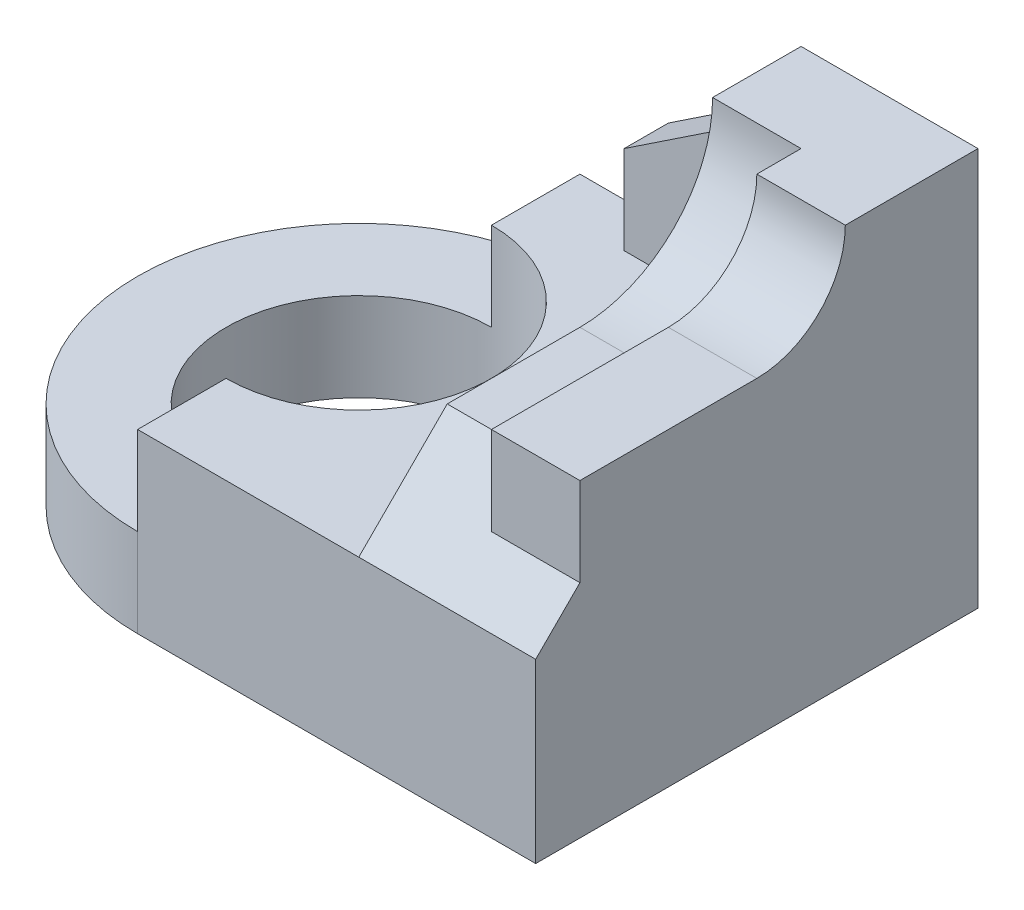
SolidWorks part; units mm, degrees
ref_plane "Front Plane" through (0, 0, 0) normal (0, 0, 1) x (1, 0, 0)
ref_plane "Top Plane" through (0, 0, 0) normal (0, 1, 0) x (1, 0, 0)
ref_plane "Right Plane" through (0, 0, 0) normal (1, 0, 0) x (0, 0, -1)
sketch "Sketch2" plane through (0, 0, 0) normal (0, 1, 0) x (1, 0, 0)
  line L1 (0, 0) -> (-140, 0)
  line L2 (0, 0) -> (0, 100)
  line L3 (0, 100) -> (-140, 100)
  line L4 (-140, 0) -> (-140, 100)
  dimension "D1" = 140
  dimension "D2" = 100
extrude "Boss-Extrude2" add sketch "Sketch2" along normal blind 90
sketch "Sketch3" plane through (0, 90, 0) normal (0, 1, 0) x (1, 0, 0)
  line L0 (0, 100) -> (-140, 100) construction
  line L1 (-140, 100) -> (-140, 0) construction
  line L4 (-90, 100) -> (-140, 100)
  line L5 (-140, 100) -> (-140, 0)
  line L6 (-140, 0) -> (-90, 0)
  arc A0 (-90, 100) -> (-90, 0) centre (-90, 50) ccw
  line M2 (0, 100) -> (-140, 100)
  line M3 (-140, 100) -> (-140, 0)
  line M4 (-140, 0) -> (0, 0)
  dimension "D1" = 50
extrude "Cut-Extrude1" cut sketch "Sketch3" against normal blind 90 contours A0 M2 M3 | A0 L5 M4
sketch "Sketch4" plane through (0, 90, 0) normal (0, 1, 0) x (1, 0, 0)
  circle A0 centre (-90, 50) radius 30
  arc A1 (-90, 100) -> (-90, 0) centre (-90, 50) ccw construction
  point P2 (-140, 50)
  dimension "D1" = 60
  dimension "D2" = 50
  dimension "D3" = 50
extrude "Cut-Extrude2" cut sketch "Sketch4" against normal blind 90
ref_plane "Plane1" through (0, 20, 0) normal (0, 1, 0) x (1, 0, 0)
sketch "Sketch5" plane through (0, 20, 0) normal (0, 1, 0) x (1, 0, 0)
  line L1 (-90, 0) -> (-140, 0)
  line L2 (-90, 0) -> (-90, 100)
  line L3 (-90, 100) -> (-140, 100)
  line L4 (-140, 0) -> (-140, 100)
  dimension "D1" = 90
  dimension "D2" = 0
  dimension "D3" = 0
  dimension "D4" = 50
extrude "Cut-Extrude3" cut sketch "Sketch5" along normal blind 90
ref_plane "Plane2" through (0, 40, 0) normal (0, 1, 0) x (1, 0, 0)
sketch "Sketch6" plane through (0, 40, 0) normal (0, 1, 0) x (1, 0, 0)
  line L0 (0, 100) -> (-90, 100) construction
  line L1 (-40, 0) -> (-90, 0)
  line L2 (-40, 0) -> (-40, 100)
  line L3 (-40, 100) -> (-90, 100)
  line L4 (-90, 0) -> (-90, 100)
  line L5 (-90, 0) -> (0, 0) construction
  dimension "D1" = 40
  dimension "D2" = 0
  dimension "D3" = 0
  dimension "D4" = 50
extrude "Cut-Extrude4" cut sketch "Sketch6" along normal blind 90
sketch "Sketch7" plane through (-40, 0, 0) normal (-1, 0, 0) x (0, 0, 1)
  line L0 (-100, 90) -> (0, 90) construction
  line L1 (-50, 60) -> (0, 60)
  line L2 (0, 90) -> (0, 40) construction
  line L3 (-80, 90) -> (0, 90)
  line L4 (0, 90) -> (0, 60)
  arc A0 (-80, 90) -> (-50, 60) centre (-50, 90) ccw
  dimension "D1" = 30
  dimension "D2" = 20
  dimension "D3" = 50
extrude "Cut-Extrude5" cut sketch "Sketch7" against normal blind 20
sketch "Sketch8" plane through (-40, 0, 0) normal (-1, 0, 0) x (0, 0, 1)
  line L0 (0, 40) -> (-20, 60)
  line L1 (-50, 60) -> (0, 60) construction
  line L2 (-20, 60) -> (0, 60)
  line L3 (0, 60) -> (0, 40)
  dimension "D1" = 20
extrude "Cut-Extrude6" cut sketch "Sketch8" against normal blind 20
sketch "Sketch9" plane through (-20, 0, 0) normal (-1, 0, 0) x (0, 0, 1)
  line L0 (0, 90) -> (-80, 90) construction
  line L1 (-50, 70) -> (-10, 70)
  line L2 (-10, 70) -> (-10, 50)
  line L3 (-20, 60) -> (0, 40) construction
  line L4 (-70, 90) -> (0, 90)
  line L5 (0, 90) -> (0, 40)
  line L6 (0, 40) -> (-10, 50)
  arc A0 (-70, 90) -> (-50, 70) centre (-50, 90) ccw
  dimension "D1" = 20
  dimension "D2" = 30
  dimension "D3" = 50
  dimension "D4" = 10
  dimension "D5" = 40
extrude "Cut-Extrude7" cut sketch "Sketch9" against normal blind 20
sketch "Sketch10" plane through (0, 0, -100) normal (0, 0, -1) x (-1, 0, 0)
  line L0 (40, 80) -> (70, 60)
  line L1 (40, 90) -> (40, 40) construction
  line L2 (70, 60) -> (70, 40)
  line L3 (40, 40) -> (90, 40) construction
  line L4 (70, 40) -> (40, 40)
  line L5 (40, 40) -> (40, 80)
  dimension "D1" = 10
  dimension "D2" = 20
  dimension "D3" = 20
extrude "Boss-Extrude3" add sketch "Sketch10" against normal blind 10
